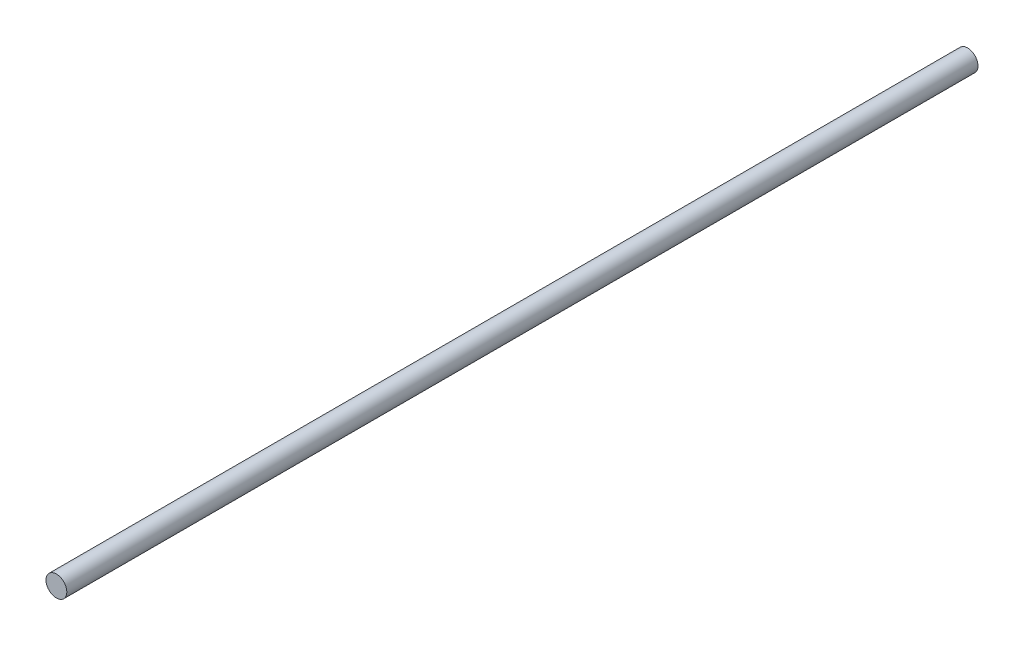
SolidWorks part; units mm, degrees
material "AISI 316 Annealed Stainless Steel Bar (SS)"
ref_plane "Front Plane" through (0, 0, 0) normal (0, 0, 1) x (1, 0, 0)
ref_plane "Top Plane" through (0, 0, 0) normal (0, 1, 0) x (1, 0, 0)
ref_plane "Right Plane" through (0, 0, 0) normal (1, 0, 0) x (0, 0, -1)
sketch "Sketch1" plane through (0, 0, 0) normal (0, 0, 1) x (1, 0, 0)
  circle A0 centre (0, 0) radius 4
  dimension "D1" = 8
extrude "Boss-Extrude1" add sketch "Sketch1" along normal blind 350
